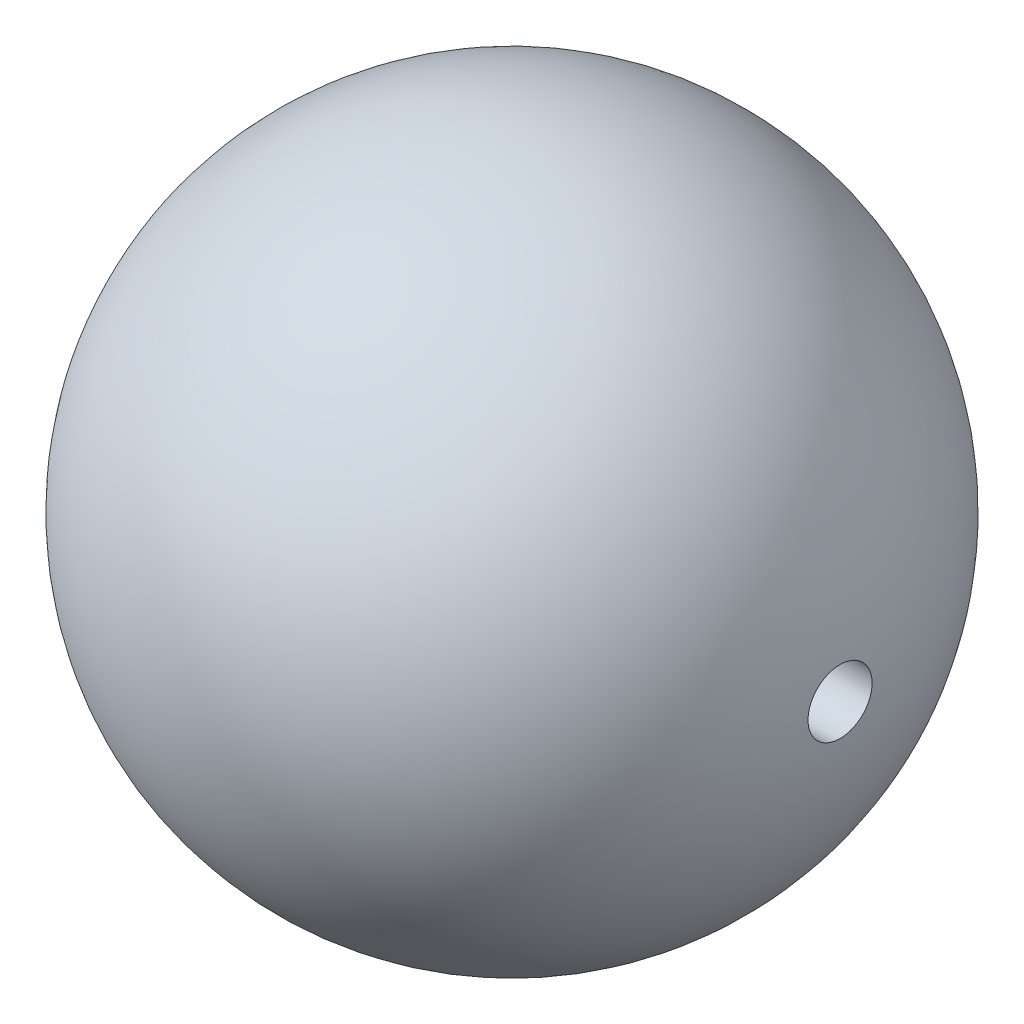
SolidWorks part; units mm, degrees
ref_plane "Alzado" through (0, 0, 0) normal (0, 0, 1) x (1, 0, 0)
ref_plane "Planta" through (0, 0, 0) normal (0, 1, 0) x (1, 0, 0)
ref_plane "Vista lateral" through (0, 0, 0) normal (1, 0, 0) x (0, 0, -1)
sketch "Croquis1" plane through (0, 0, 0) normal (0, 1, 0) x (1, 0, 0)
  line L0 (-6.7899, 0) -> (-18, 0)
  line L2 (17.9147, 1.75) -> (-6.7899, 1.75)
  line L5 (-6.7899, 0) -> (-6.7899, 1.75)
  arc A0 (17.9147, 1.75) -> (-18, 0) centre (0, 0) ccw
revolve "Revolución2" add sketch "Croquis1" angle 360 about L0
